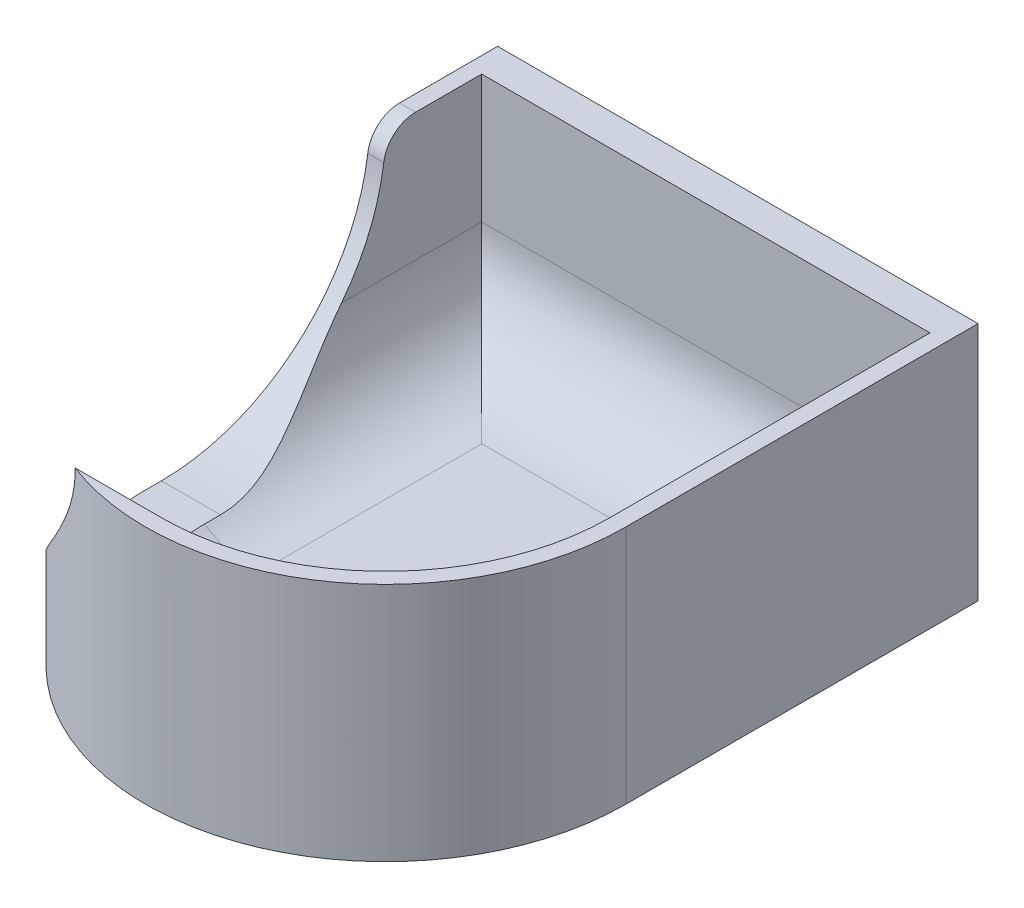
SolidWorks part; units mm, degrees
ref_plane "Front Plane" through (0, 0, 0) normal (0, 0, 1) x (1, 0, 0)
ref_plane "Top Plane" through (0, 0, 0) normal (0, 1, 0) x (1, 0, 0)
ref_plane "Right Plane" through (0, 0, 0) normal (1, 0, 0) x (0, 0, -1)
sketch "Sketch1" plane through (0, 0, 0) normal (0, 1, 0) x (1, 0, 0)
  line L1 (0, 0) -> (38.1, 0)
  line L2 (0, 0) -> (0, -25.4)
  line L4 (38.1, 0) -> (38.1, -25.4)
  arc A0 (0, -25.4) -> (38.1, -25.4) centre (19.05, -25.4) ccw
  dimension "D1" = 38.1
  dimension "D2" = 25.4
extrude "Boss-Extrude1" add sketch "Sketch1" along normal blind 1.27
sketch "Sketch3" plane through (0, 1.27, 0) normal (0, 1, 0) x (1, 0, 0)
  line L0 (0, 0) -> (0, -25.4) construction
  line L1 (38.1, -25.4) -> (38.1, 0) construction
  line L2 (0, 0) -> (0, -25.4)
  line L3 (38.1, -25.4) -> (38.1, 0)
  line L4 (0, 0) -> (1.27, 0)
  line L5 (38.1, 0) -> (36.83, 0)
  line L6 (1.27, 0) -> (1.27, -25.4)
  line L7 (36.83, 0) -> (36.83, -25.4)
  arc A0 (0, -25.4) -> (38.1, -25.4) centre (19.05, -25.4) ccw construction
  arc A1 (0, -25.4) -> (38.1, -25.4) centre (19.05, -25.4) ccw
  arc A2 (1.27, -25.4) -> (36.83, -25.4) centre (19.05, -25.4) ccw
  dimension "D1" = 25.4
  dimension "D2" = 1.27
extrude "Boss-Extrude3" add sketch "Sketch3" along normal blind 17.78
sketch "Sketch5" plane through (0, 0, 0) normal (0, 0, -1) x (-1, 0, 0)
  line L1 (-38.1, 19.05) -> (0, 19.05)
  line L2 (-38.1, 19.05) -> (-38.1, 0)
  line L3 (-38.1, 0) -> (0, 0)
  line L4 (0, 19.05) -> (0, 0)
extrude "Boss-Extrude4" add sketch "Sketch5" along normal blind 2.54
sketch "Sketch4" plane through (38.1, 0, 0) normal (1, 0, 0) x (0, 0, -1)
  line L1 (-2.54, 19.05) -> (0, 19.05)
  line L2 (-2.54, 19.05) -> (-2.54, 16.51)
  line L3 (-2.54, 16.51) -> (0, 16.51)
  line L4 (0, 19.05) -> (0, 16.51)
  line L5 (2.54, 19.05) -> (2.54, 0) construction
  dimension "D1" = 2.54
  dimension "D2" = 2.54
  dimension "D3" = 2.54
extrude "Cut-Extrude1" [suppressed] cut sketch "Sketch4" against normal through all
fillet "Fillet1" radius 7.62 4 edges at (19.05, 1.27, 43.18)
sketch "Sketch7" [suppressed] plane through (0, 0, 0) normal (0, 0, 1) x (1, 0, 0)
  line L0 (38.1, 19.05) -> (0, 19.05) construction
  circle A0 centre (19.05, 19.05) radius 15.24
  dimension "D1" = 30.48
extrude "Cut-Extrude3" [suppressed] cut sketch "Sketch7" along normal through all
sketch "Sketch9" plane through (0, 0, 0) normal (-1, 0, 0) x (0, 0, 1)
  line L0 (24.13, 19.05) -> (26.67, 19.05) construction
  line L1 (24.13, 35.56) -> (26.67, 35.56)
  line L2 (24.13, 2.54) -> (26.67, 2.54)
  arc A0 (24.13, 35.56) -> (24.13, 2.54) centre (24.13, 19.05) ccw
  arc A1 (26.67, 2.54) -> (26.67, 35.56) centre (26.67, 19.05) ccw
  point P2 (25.4, 19.05)
  dimension "D1" = 16.51
  dimension "D2" = 2.54
extrude "Cut-Extrude5" cut sketch "Sketch9" against normal up to next
fillet "Fillet3" radius 2.54 1 edges at (0.635, 19.05, 7.62)
